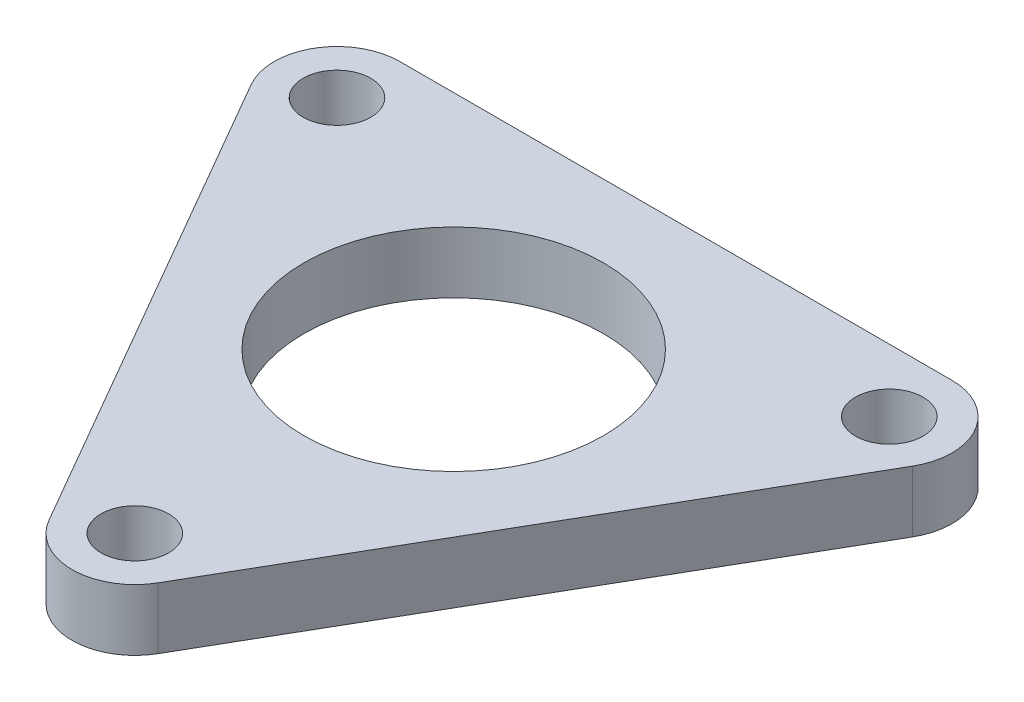
SolidWorks part; units mm, degrees
material "1023 Carbon Steel Sheet (SS)"
ref_plane "Front Plane" through (0, 0, 0) normal (0, 0, 1) x (1, 0, 0)
ref_plane "Top Plane" through (0, 0, 0) normal (0, 1, 0) x (1, 0, 0)
ref_plane "Right Plane" through (0, 0, 0) normal (1, 0, 0) x (0, 0, -1)
sketch "Sketch1" plane through (0, 0, 0) normal (0, 1, 0) x (1, 0, 0)
  line L0 (0, 16.5) -> (-14.2894, 8.25) construction
  line L1 (-14.2894, 8.25) -> (-14.2894, -8.25) construction
  line L2 (-17.104, 6.625) -> (-2.8146, -18.125)
  line L3 (2.8146, -18.125) -> (17.104, 6.625)
  line L4 (-14.2894, 11.5) -> (14.2894, 11.5)
  circle A0 centre (0, 0) radius 19.75 construction
  circle A1 centre (0, 0) radius 16.5 construction
  circle A2 centre (0, 0) radius 7.75
  circle A3 centre (0, 16.5) radius 1.75 construction
  circle A4 centre (-14.2894, 8.25) radius 1.75
  circle A5 centre (-14.2894, -8.25) radius 1.75 construction
  circle A6 centre (0, -16.5) radius 1.75
  circle A7 centre (14.2894, -8.25) radius 1.75 construction
  circle A8 centre (14.2894, 8.25) radius 1.75
  arc A9 (-14.2894, 11.5) -> (-17.104, 6.625) centre (-14.2894, 8.25) ccw
  arc A10 (17.104, 6.625) -> (14.2894, 11.5) centre (14.2894, 8.25) ccw
  arc A11 (-2.8146, -18.125) -> (2.8146, -18.125) centre (0, -16.5) ccw
  dimension "D1" = 39.5
  dimension "D2" = 33
  dimension "D3" = 15.5
  dimension "D4" = 3.5
extrude "Boss-Extrude1" add sketch "Sketch1" along normal blind 3.175
